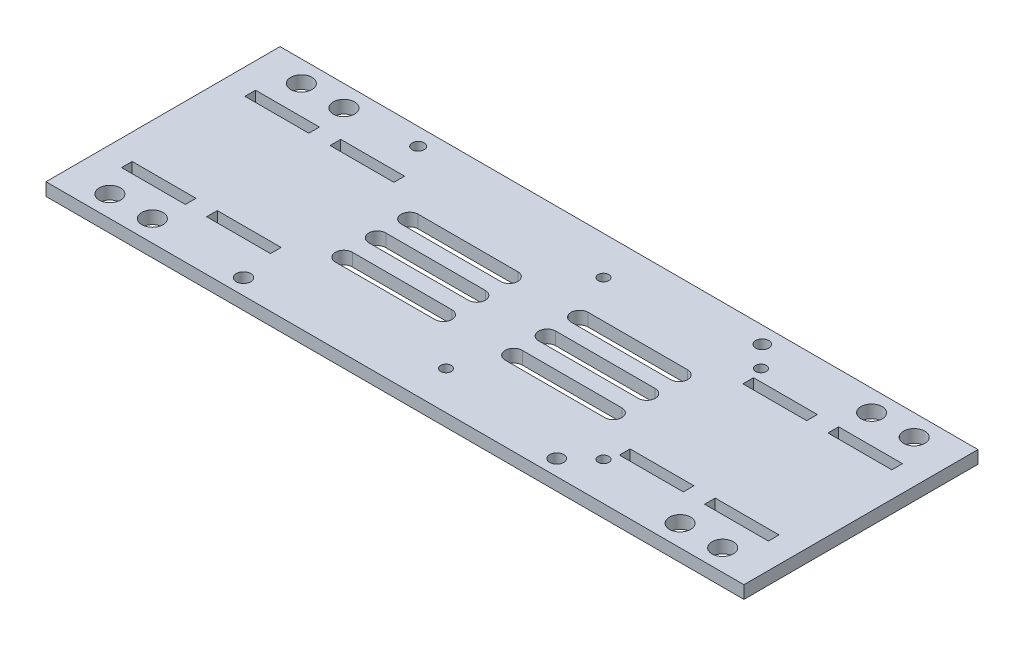
SolidWorks part; units mm, degrees
ref_plane "Front Plane" through (0, 0, 0) normal (0, 0, 1) x (1, 0, 0)
ref_plane "Top Plane" through (0, 0, 0) normal (0, 1, 0) x (1, 0, 0)
ref_plane "Right Plane" through (0, 0, 0) normal (1, 0, 0) x (0, 0, -1)
sketch "Sketch1" plane through (0, 0, 0) normal (0, 1, 0) x (1, 0, 0)
  line L0 (0, -5.7309) -> (0, 9.5321) construction
  line L1 (82, 27.5) -> (-82, 27.5)
  line L2 (82, 27.5) -> (82, -27.5)
  line L3 (82, -27.5) -> (-82, -27.5)
  line L4 (-82, 27.5) -> (-82, -27.5)
  line L6 (56, 15.75) -> (41, 15.75)
  line L7 (56, 15.75) -> (56, 13.25)
  line L8 (56, 13.25) -> (41, 13.25)
  line L9 (41, 15.75) -> (41, 13.25)
  line L10 (76, 15.75) -> (61, 15.75)
  line L11 (76, 15.75) -> (76, 13.25)
  line L12 (76, 13.25) -> (61, 13.25)
  line L13 (61, 15.75) -> (61, 13.25)
  line L15 (-7.975, 0) -> (11.9988, 0) construction
  line L19 (61, -15.75) -> (61, -13.25)
  line L20 (76, -13.25) -> (61, -13.25)
  line L21 (76, -15.75) -> (76, -13.25)
  line L22 (76, -15.75) -> (61, -15.75)
  line L23 (41, -15.75) -> (41, -13.25)
  line L24 (56, -13.25) -> (41, -13.25)
  line L25 (56, -15.75) -> (56, -13.25)
  line L26 (56, -15.75) -> (41, -15.75)
  line L28 (-56, -15.75) -> (-41, -15.75)
  line L29 (-56, -15.75) -> (-56, -13.25)
  line L30 (-56, -13.25) -> (-41, -13.25)
  line L31 (-41, -15.75) -> (-41, -13.25)
  line L32 (-76, -15.75) -> (-61, -15.75)
  line L33 (-76, -15.75) -> (-76, -13.25)
  line L34 (-76, -13.25) -> (-61, -13.25)
  line L35 (-61, -15.75) -> (-61, -13.25)
  line L40 (-61, 15.75) -> (-61, 13.25)
  line L41 (-76, 13.25) -> (-61, 13.25)
  line L42 (-76, 15.75) -> (-76, 13.25)
  line L43 (-76, 15.75) -> (-61, 15.75)
  line L44 (-41, 15.75) -> (-41, 13.25)
  line L45 (-56, 13.25) -> (-41, 13.25)
  line L46 (-56, 15.75) -> (-56, 13.25)
  line L47 (-56, 15.75) -> (-41, 15.75)
  dimension "D4" = 2.5
  dimension "D5" = 15
  dimension "D6" = 15
  dimension "D7" = 2.5
  dimension "D10" = 164
  dimension "D11" = 82
  dimension "D12" = 55
  dimension "D13" = 27.5
  dimension "D20" = 2.5
extrude "Boss-Extrude1" add sketch "Sketch1" along normal blind 3
sketch "Sketch2" plane through (0, 3, 0) normal (0, 1, 0) x (1, 0, 0)
  line L0 (-31.6585, 2) -> (-8.2664, 2)
  line L1 (31.6585, -9.8567) -> (8.2664, -9.8567)
  line L2 (31.6585, -5.8567) -> (8.2664, -5.8567)
  line L4 (-31.6585, -2) -> (-8.2664, -2)
  line L5 (-31.6585, 9.6208) -> (-8.2664, 9.6208)
  line L6 (-31.6585, 5.6208) -> (-8.2664, 5.6208)
  line L7 (31.6585, 5.6208) -> (8.2664, 5.6208)
  line L8 (31.6585, 9.6208) -> (8.2664, 9.6208)
  line L9 (-31.6585, -5.8567) -> (-8.2664, -5.8567)
  line L10 (31.6585, -2) -> (8.2664, -2)
  line L11 (31.6585, 2) -> (8.2664, 2)
  line L12 (-31.6585, -9.8567) -> (-8.2664, -9.8567)
  line L15 (0, 0) -> (-4.1634, 0) construction
  arc A0 (31.6585, -9.8567) -> (31.6585, -5.8567) centre (31.6585, -7.8567) ccw
  arc A1 (8.2664, -5.8567) -> (8.2664, -9.8567) centre (8.2664, -7.8567) ccw
  arc A2 (-8.2664, 2) -> (-8.2664, -2) centre (-8.2664, 0) cw
  arc A3 (-31.6585, -2) -> (-31.6585, 2) centre (-31.6585, 0) cw
  arc A4 (31.6585, 5.6208) -> (31.6585, 9.6208) centre (31.6585, 7.6208) ccw
  arc A5 (8.2664, 9.6208) -> (8.2664, 5.6208) centre (8.2664, 7.6208) ccw
  arc A6 (31.6585, -2) -> (31.6585, 2) centre (31.6585, 0) ccw
  arc A7 (8.2664, 2) -> (8.2664, -2) centre (8.2664, 0) ccw
  arc A8 (-8.2664, 9.6208) -> (-8.2664, 5.6208) centre (-8.2664, 7.6208) cw
  arc A9 (-31.6585, 5.6208) -> (-31.6585, 9.6208) centre (-31.6585, 7.6208) cw
  arc A10 (-8.2664, -5.8567) -> (-8.2664, -9.8567) centre (-8.2664, -7.8567) cw
  arc A11 (-31.6585, -9.8567) -> (-31.6585, -5.8567) centre (-31.6585, -7.8567) cw
extrude "Cut-Extrude1" cut sketch "Sketch2" against normal blind 3
sketch "Sketch3" plane through (0, 3, 0) normal (0, 1, 0) x (1, 0, 0)
  circle A0 centre (40, 18.5) radius 1.25
  circle A1 centre (40, -18.5) radius 1.25
  circle A2 centre (3, -18.5) radius 1.25
  circle A3 centre (3, 18.5) radius 1.25
  dimension "D1" = 18.5
  dimension "D2" = 3
  dimension "D3" = 2.5
  dimension "D4" = 2.5
  dimension "D5" = 2.5
  dimension "D6" = 2.5
extrude "Cut-Extrude2" cut sketch "Sketch3" against normal blind 10
sketch "Sketch4" plane through (0, 3, 0) normal (0, 1, 0) x (1, 0, 0)
  line L16 (82, -27.5) -> (82, 27.5) construction
  line L26 (-82, -27.5) -> (82, -27.5) construction
  line L30 (63.8385, 0) -> (72.3938, 0) construction
  line L31 (-82, 27.5) -> (-82, -27.5) construction
  line L34 (82, 27.5) -> (-82, 27.5) construction
  circle A0 centre (72, -22.5) radius 2.5
  circle A1 centre (62, -22.5) radius 2.5
  circle A2 centre (72, 22.5) radius 2.5
  circle A3 centre (62, 22.5) radius 2.5
  circle A4 centre (-72, 22.5) radius 2.5
  circle A5 centre (-62, 22.5) radius 2.5
  circle A6 centre (-72, -22.5) radius 2.5
  circle A7 centre (-62, -22.5) radius 2.5
  point P0 (-78, 0)
  point P2 (59, 0)
  point P7 (-59, 0)
  point P15 (78, 0)
  point P24 (78, 0)
  dimension "D3" = 10
  dimension "D5" = 5
  dimension "D7" = 10
  dimension "D8" = 5
  dimension "D9" = 5
  dimension "D10" = 5
  dimension "D11" = 10
  dimension "D12" = 5
  dimension "D13" = 10
  dimension "D14" = 5
  dimension "D15" = 5
  dimension "D16" = 5
  dimension "D17" = 5
  dimension "D18" = 5
  dimension "D19" = 10
  dimension "D20" = 10
  dimension "D21" = 5
  dimension "D22" = 5
extrude "Cut-Extrude3" cut sketch "Sketch4" against normal through all
sketch "Sketch5" plane through (0, 3, 0) normal (0, 1, 0) x (1, 0, 0)
  circle A0 centre (34.3231, -23.8155) radius 1.6358
  circle A1 centre (35.2358, 23.5655) radius 1.5508
  circle A2 centre (-45.4844, 23.4378) radius 1.4101
  circle A3 centre (-39.2763, -23.8155) radius 1.6925
extrude "Cut-Extrude4" cut sketch "Sketch5" against normal through all
